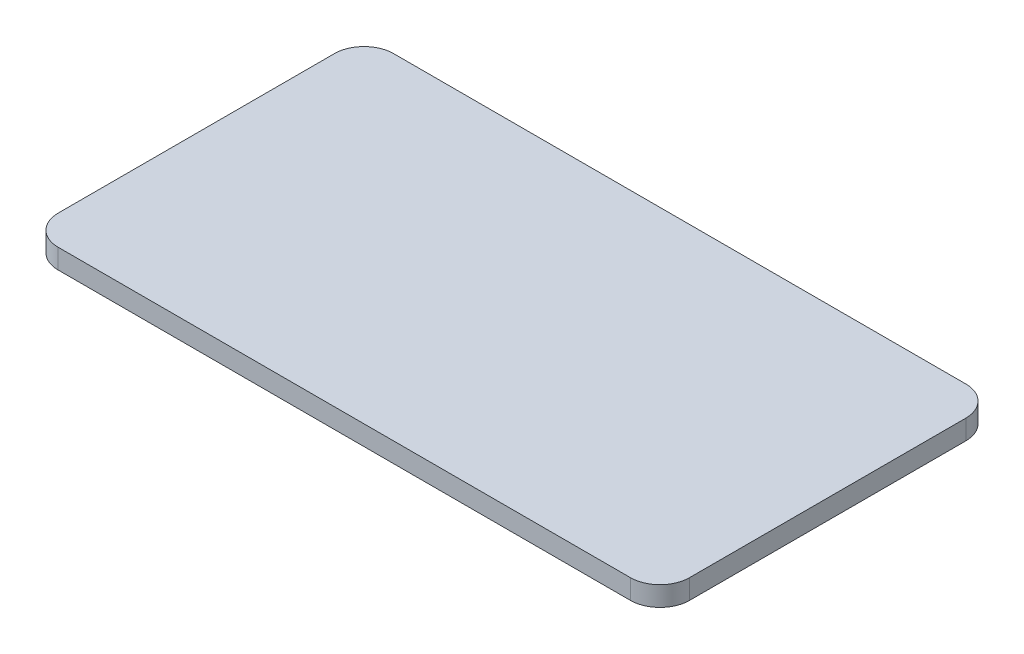
SolidWorks part; units mm, degrees
ref_plane "Front Plane" through (0, 0, 0) normal (0, 0, 1) x (1, 0, 0)
ref_plane "Top Plane" through (0, 0, 0) normal (0, 1, 0) x (1, 0, 0)
ref_plane "Right Plane" through (0, 0, 0) normal (1, 0, 0) x (0, 0, -1)
sketch "Sketch1" plane through (0, 0, 0) normal (0, 1, 0) x (1, 0, 0)
  line L1 (3, 0) -> (61, 0)
  line L2 (0, 3) -> (0, 31)
  line L3 (3, 34) -> (61, 34)
  line L4 (64, 3) -> (64, 31)
  arc A0 (3, 0) -> (0, 3) centre (3, 3) cw
  arc A1 (61, 0) -> (64, 3) centre (61, 3) ccw
  arc A2 (61, 34) -> (64, 31) centre (61, 31) cw
  arc A3 (0, 31) -> (3, 34) centre (3, 31) cw
  point P7 (0, 0)
  point P12 (64, 34)
  point P15 (0, 34)
  dimension "D3" = 3
  dimension "D1" = 34
  dimension "D2" = 64
extrude "Boss-Extrude1" add sketch "Sketch1" along normal blind 2
